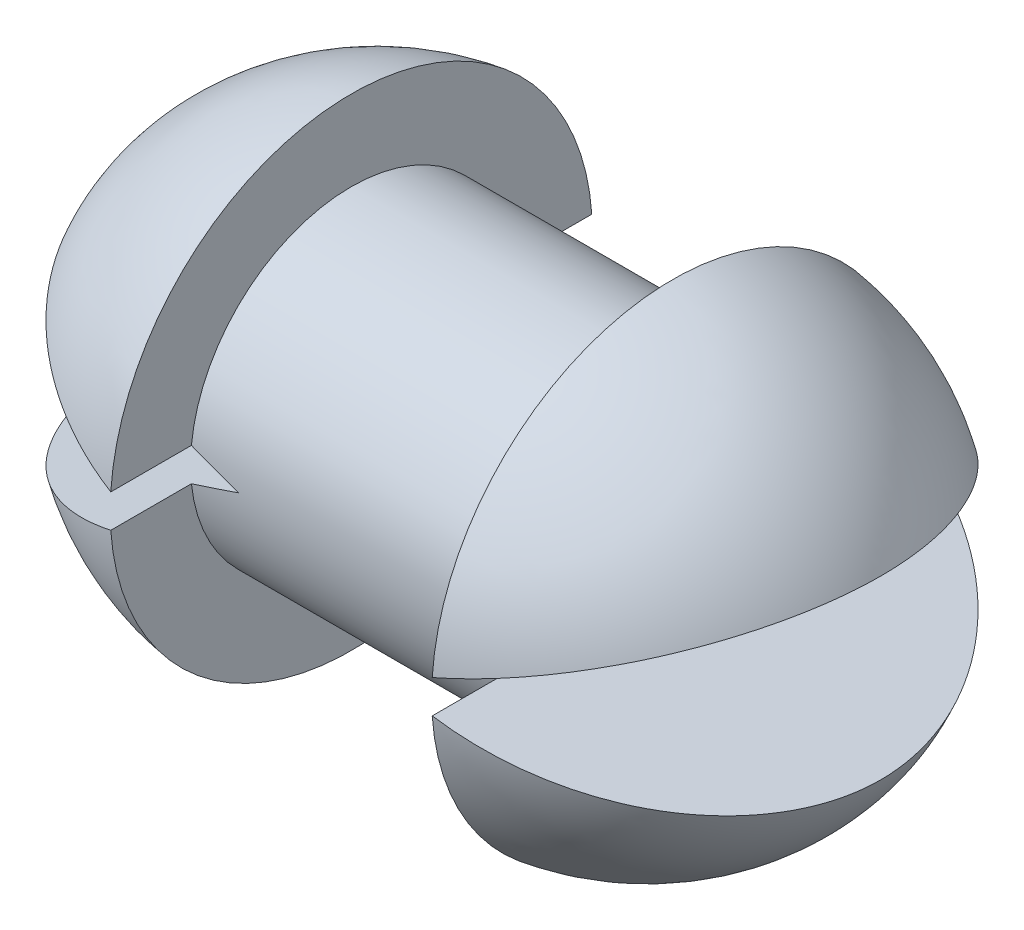
SolidWorks part; units mm, degrees
ref_plane "Front Plane" through (0, 0, 0) normal (0, 0, 1) x (1, 0, 0)
ref_plane "Top Plane" through (0, 0, 0) normal (0, 1, 0) x (1, 0, 0)
ref_plane "Right Plane" through (0, 0, 0) normal (1, 0, 0) x (0, 0, -1)
sketch "Sketch1" plane through (0, 0, 0) normal (0, 0, 1) x (1, 0, 0)
  line L0 (0, -29.1631) -> (0, 41.977) construction
  line L1 (-10, 10) -> (10, 10)
  line L2 (10, 10) -> (10, 15)
  line L3 (24.5, 0) -> (7, 0)
  line L4 (-3.1225, 0) -> (36.3968, 0) construction
  line L5 (7, 0) -> (-7, 0)
  line L6 (0, 0) -> (7, 0)
  line L7 (-24.5, 0) -> (-7, 0)
  line L8 (-10, 10) -> (-10, 15)
  arc A0 (10, 15) -> (24.5, 0) centre (7.5987, -1.8296) cw
  arc A1 (-10, 15) -> (-24.5, 0) centre (-7.5987, -1.8296) ccw
  point P17 (0, 10)
  dimension "D7" = 17
  dimension "D8" = 10
  dimension "D2" = 24.5
  dimension "D3" = 10
  dimension "D4" = 0
  dimension "D5" = 15
  dimension "D6" = 7
revolve "Revolve4" add sketch "Sketch1" angle 360 about L4
sketch "Sketch2" plane through (0, 0, 0) normal (0, 0, 1) x (1, 0, 0)
  line L0 (26.1527, 0) -> (-4.9101, 0) construction
  line L1 (0, 6.6157) -> (0, -5.9438) construction
  line L2 (7, 0) -> (24.9649, 6.1858)
  line L3 (24.9649, 6.1858) -> (25, 0)
  line L4 (25, 0) -> (7, 0)
  line L5 (24.9649, -6.1858) -> (25, 0)
  line L6 (7, 0) -> (24.9649, -6.1858)
  line L7 (-24.9649, -6.1858) -> (-25, 0)
  line L8 (-7, 0) -> (-24.9649, -6.1858)
  line L9 (-24.9649, 6.1858) -> (-25, 0)
  line L10 (-7, 0) -> (-24.9649, 6.1858)
  line L11 (-25, 0) -> (-7, 0)
  dimension "D1" = 7
  dimension "D2" = 19
  dimension "D3" = 19
  dimension "D4" = 25
extrude "Cut-Extrude1" cut sketch "Sketch2" against normal mid plane 40 contours L11 L7 L8 | L9 L11 L10 | L4 L3 L2 | L4 L6 L5
